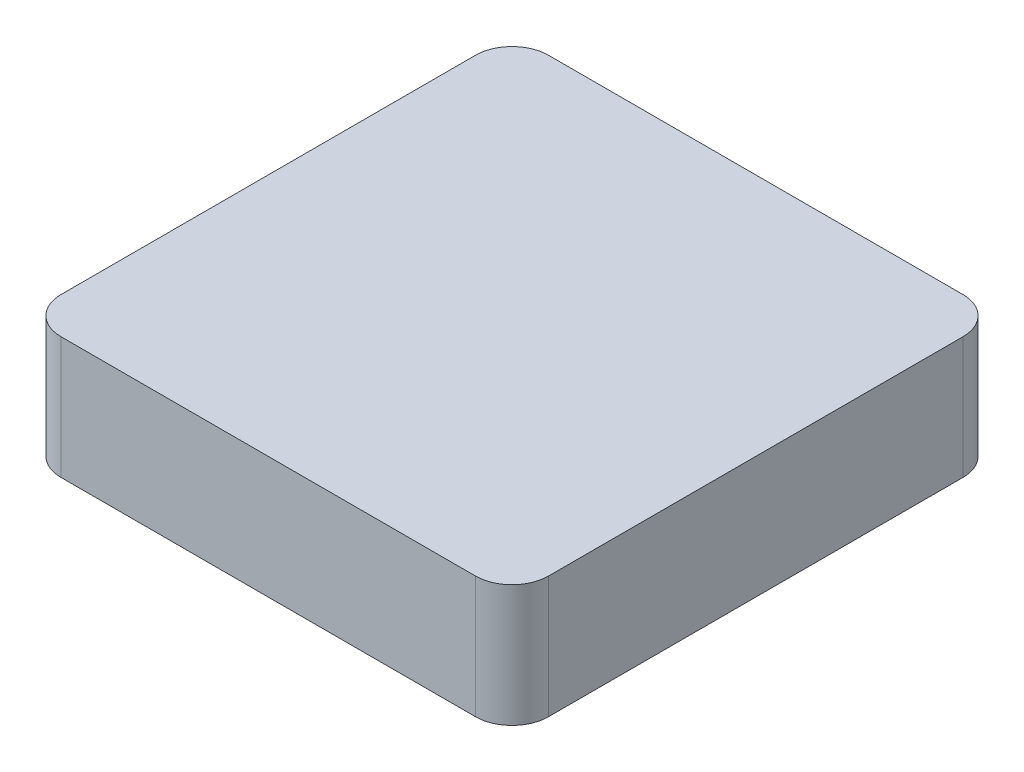
SolidWorks part; units mm, degrees
ref_plane "Front Plane" through (0, 0, 0) normal (0, 0, 1) x (1, 0, 0)
ref_plane "Top Plane" through (0, 0, 0) normal (0, 1, 0) x (1, 0, 0)
ref_plane "Right Plane" through (0, 0, 0) normal (1, 0, 0) x (0, 0, -1)
sketch "Sketch1" plane through (0, 0, 0) normal (0, 1, 0) x (1, 0, 0)
  line L1 (-8.5, -10) -> (8.5, -10)
  line L2 (-10, -8.5) -> (-10, 8.5)
  line L3 (-8.5, 10) -> (8.5, 10)
  line L4 (10, -8.5) -> (10, 8.5)
  line L5 (-10, -10) -> (10, 10) construction
  line L6 (-10, 10) -> (10, -10) construction
  arc A0 (-10, 8.5) -> (-8.5, 10) centre (-8.5, 8.5) cw
  arc A1 (-8.5, -10) -> (-10, -8.5) centre (-8.5, -8.5) cw
  arc A2 (8.5, -10) -> (10, -8.5) centre (8.5, -8.5) ccw
  arc A3 (8.5, 10) -> (10, 8.5) centre (8.5, 8.5) cw
  point P0 (0, 0)
  dimension "D3" = 1.5
  dimension "D1" = 20
  dimension "D2" = 20
extrude "Boss-Extrude1" add sketch "Sketch1" along normal blind 5
